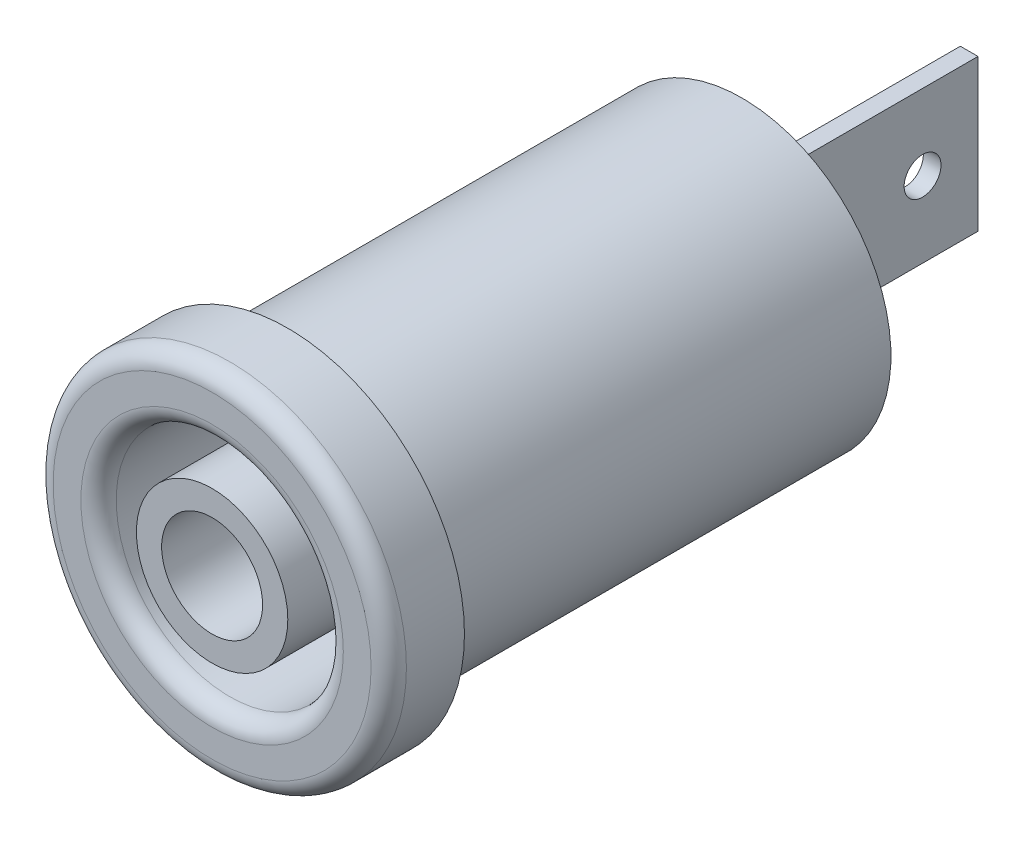
SolidWorks part; units mm, degrees
ref_plane "Front Plane" through (0, 0, 0) normal (0, 0, 1) x (1, 0, 0)
ref_plane "Top Plane" through (0, 0, 0) normal (0, 1, 0) x (1, 0, 0)
ref_plane "Right Plane" through (0, 0, 0) normal (1, 0, 0) x (0, 0, -1)
sketch "Sketch1" plane through (0, 0, 0) normal (0, 0, 1) x (1, 0, 0)
  circle A0 centre (0, 0) radius 7
  dimension "D1" = 14
extrude "Boss-Extrude1" add sketch "Sketch1" along normal blind 3
sketch "Sketch2" plane through (0, 0, 0) normal (0, 0, -1) x (-1, 0, 0)
  circle A0 centre (0, 0) radius 5.9
  dimension "D1" = 11.8
extrude "Boss-Extrude2" add sketch "Sketch2" along normal blind 18
sketch "Sketch3" plane through (0, 0, -18) normal (0, 0, -1) x (-1, 0, 0)
  line L0 (0, 1.6278) -> (0, -1.3249) construction
  line L2 (-0.35, 3) -> (0.35, 3)
  line L3 (-0.35, 3) -> (-0.35, -3)
  line L4 (-0.35, -3) -> (0.35, -3)
  line L5 (0.35, 3) -> (0.35, -3)
  line L6 (0, -3) -> (0, 3) construction
  line L7 (-0.35, 0) -> (0.35, 0) construction
  point P3 (0, 0)
  dimension "D1" = 6
  dimension "D2" = 0.7
extrude "Boss-Extrude3" add sketch "Sketch3" along normal blind 9
sketch "Sketch4" plane through (0.35, 0, 0) normal (1, 0, 0) x (0, 0, -1)
  circle A0 centre (24.8028, 0) radius 0.731
extrude "Cut-Extrude1" cut sketch "Sketch4" against normal blind 0.7
sketch "Sketch8" plane through (0, 0, 3) normal (0, 0, 1) x (1, 0, 0)
  circle A0 centre (0, 0) radius 4.5
  dimension "D1" = 9
extrude "Cut-Extrude2" cut sketch "Sketch8" against normal blind 10
sketch "Sketch9" plane through (0, 0, -7) normal (0, 0, 1) x (1, 0, 0)
  circle A0 centre (0, 0) radius 3
  dimension "D1" = 6
extrude "Boss-Extrude4" add sketch "Sketch9" along normal blind 10
sketch "Sketch10" plane through (0, 0, 3) normal (0, 0, 1) x (1, 0, 0)
  circle A0 centre (0, 0) radius 2
  dimension "D1" = 4
extrude "Cut-Extrude3" cut sketch "Sketch10" against normal blind 10
fillet "Fillet3" radius 0.7 2 edges at (4.5, 0, 3) (7, 0, 3)
